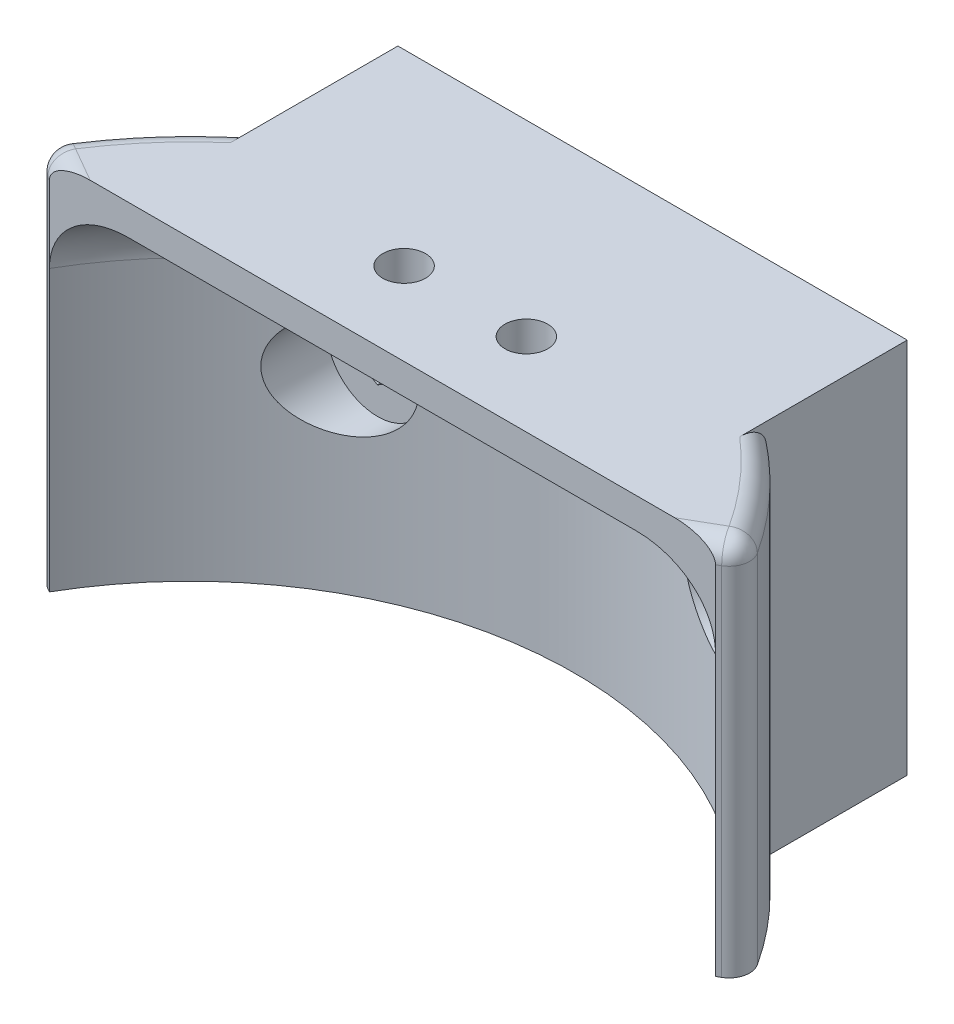
SolidWorks part; units mm, degrees
ref_plane "Front Plane" through (0, 0, 0) normal (0, 0, 1) x (1, 0, 0)
ref_plane "Top Plane" through (0, 0, 0) normal (0, 1, 0) x (1, 0, 0)
ref_plane "Right Plane" through (0, 0, 0) normal (1, 0, 0) x (0, 0, -1)
sketch "Sketch2" plane through (0, 0, 0) normal (0, 1, 0) x (1, 0, 0)
  line L0 (-32.6925, 18.875) -> (32.618, 19.0034) construction
  line L2 (32.6925, 18.875) -> (34.8575, 20.125)
  line L3 (-34.8575, 20.125) -> (-32.6925, 18.875)
  line L6 (-25, 31.5446) -> (-25, 40.3907)
  line L7 (-25, 40.3907) -> (25, 40.3907)
  line L8 (25, 31.5446) -> (25, 40.3907)
  arc A2 (34.8575, 20.125) -> (25, 31.5446) centre (0, 0) ccw
  arc A3 (32.6925, 18.875) -> (-32.6925, 18.875) centre (0, 0) ccw
  arc A4 (-25, 31.5446) -> (-34.8575, 20.125) centre (0, 0) ccw
  point P10 (-0.0372, 18.9392)
  point P11 (0, 40.3907)
  point P12 (0, 37.75)
  dimension "D3" = 37.75
  dimension "D4" = 40.25
  dimension "D1" = 50
  dimension "D2" = 2.6407
  dimension "D5" = 18.9392
extrude "Boss-Extrude2" add sketch "Sketch2" along normal blind 37
sketch "Sketch4" plane through (0, 37, 0) normal (0, 1, 0) x (1, 0, 0)
  line L0 (-32.6925, 18.875) -> (32.6925, 18.875)
  line L1 (-34.8575, 20.125) -> (-32.6925, 18.875) construction
  line L4 (32.6925, 18.875) -> (34.8575, 20.125)
  line L5 (-34.8575, 20.125) -> (-32.6925, 18.875)
  line L6 (32.6925, 18.875) -> (34.8575, 20.125) construction
  arc A0 (34.8575, 20.125) -> (25, 31.5446) centre (0, 0) ccw construction
  arc A1 (32.6925, 18.875) -> (-32.6925, 18.875) centre (0, 0) ccw construction
  arc A5 (34.8575, 20.125) -> (-34.8575, 20.125) centre (0, 0) ccw
extrude "Boss-Extrude4" add sketch "Sketch4" against normal blind 3
fillet "Fillet1" radius 6.5 1 edges at (0, 34, -37.75)
sketch "Sketch5" plane through (0, 34, 0) normal (0, -1, 0) x (-1, 0, 0)
  line L0 (-39.8345, 37.5) -> (34.489, 37.5) construction
  line L1 (-6, 27) -> (6, 27) construction
  circle A0 centre (-6, 27) radius 2.1
  circle A1 centre (6, 27) radius 2.1
  circle A2 centre (0, 0) radius 37.5 construction
  point P9 (0, 27)
  dimension "D1" = 4.2
  dimension "D2" = 4.2
  dimension "D4" = 75
  dimension "D3" = 12
  dimension "D5" = 10.5
extrude "Cut-Extrude1" cut sketch "Sketch5" against normal blind 5
sketch "Sketch6" plane through (0, 0, -40.3907) normal (0, 0, -1) x (-1, 0, 0)
  line L0 (-23.1, 35.25) -> (-23.1, 1.75)
  line L1 (-23.1, 35.25) -> (23.1, 35.25)
  line L4 (23.1, 35.25) -> (23.1, 1.75)
  line L21 (-25, 37) -> (25, 37)
  line L22 (-25, 37) -> (-25, 0)
  line L23 (-25, 0) -> (25, 0)
  line L24 (25, 37) -> (25, 0)
  line L25 (-23.1, 1.75) -> (23.1, 1.75)
  line L26 (-25, 0) -> (25, 0) construction
  line L27 (25, 37) -> (25, 0) construction
  point P7 (0, 37)
  point P9 (0, 35.25)
  point P15 (-25, 18.5)
  point P16 (-23.1, 18.5)
  dimension "D1" = 46.2
  dimension "D2" = 33.5
extrude "Boss-Extrude5" add sketch "Sketch6" along normal blind 5
sketch "Sketch7" plane through (0, 0, -40.3907) normal (0, 0, -1) x (-1, 0, 0)
  line L1 (23.1, 1.75) -> (23.1, 35.25) construction
  line L2 (-25, 18.5) -> (25, 18.5) construction
  line L3 (-25, 37) -> (-25, 0) construction
  line L4 (25, 37) -> (25, 0) construction
  line L5 (-23.1, 35.25) -> (-23.1, 1.75) construction
  circle A0 centre (-18, 18.5) radius 1.1
  circle A1 centre (18, 18.5) radius 1.1
  dimension "D1" = 2.2
  dimension "D2" = 2.2
  dimension "D3" = 5.1
  dimension "D4" = 5.1
extrude "Cut-Extrude2" cut sketch "Sketch7" against normal blind 1
sketch "Sketch8" plane through (0, 0, -39.3907) normal (0, 0, -1) x (-1, 0, 0)
  line L1 (-16, 17.3453) -> (-16, 19.6547)
  line L2 (-16, 19.6547) -> (-18, 20.8094)
  line L3 (-18, 20.8094) -> (-20, 19.6547)
  line L4 (-20, 19.6547) -> (-20, 17.3453)
  line L5 (-20, 17.3453) -> (-18, 16.1906)
  line L6 (-18, 16.1906) -> (-16, 17.3453)
  line L7 (20, 17.3453) -> (20, 19.6547)
  line L8 (20, 19.6547) -> (18, 20.8094)
  line L9 (18, 20.8094) -> (16, 19.6547)
  line L10 (16, 19.6547) -> (16, 17.3453)
  line L11 (16, 17.3453) -> (18, 16.1906)
  line L12 (18, 16.1906) -> (20, 17.3453)
  circle A0 centre (-18, 18.5) radius 2 construction
  circle A3 centre (-18, 18.5) radius 1.1 construction
  circle A4 centre (-18, 18.5) radius 1.1 construction
  circle A5 centre (18, 18.5) radius 1.1 construction
  circle A6 centre (18, 18.5) radius 1.1 construction
  circle A7 centre (18, 18.5) radius 2 construction
  dimension "D1" = 4
  dimension "D2" = 4
extrude "Cut-Extrude3" cut sketch "Sketch8" against normal blind 3
sketch "Sketch9" plane through (0, 0, -36.3907) normal (0, 0, -1) x (-1, 0, 0)
  circle A0 centre (-18, 18.5) radius 5
  circle A1 centre (18, 18.5) radius 5
  dimension "D1" = 10
extrude "Cut-Extrude4" cut sketch "Sketch9" against normal through all
fillet "Fillet2" radius 2 6 edges at (34.8575, 18.5, -20.125) (33.775, 37, -19.5) (30.4686, 37, -26.3008) (-34.8575, 18.5, -20.125) (-33.775, 37, -19.5) (-30.4686, 37, -26.3008)
